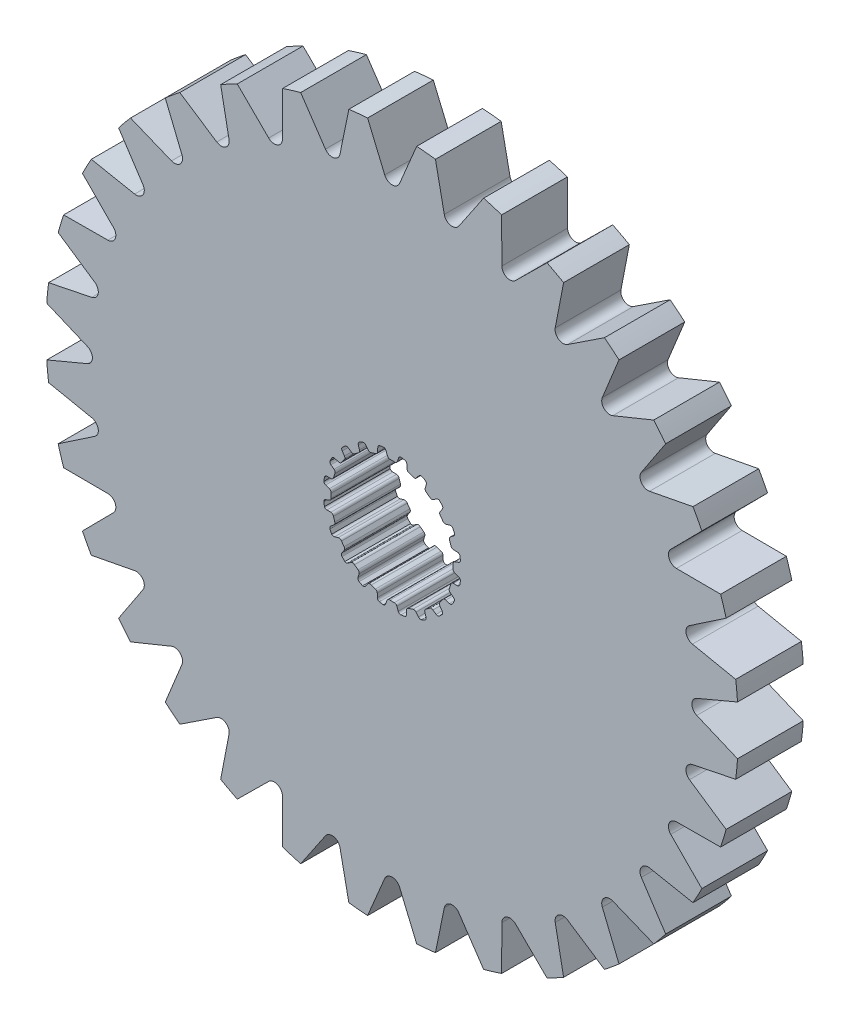
SolidWorks part; units mm, degrees
ref_plane "Front Plane" through (0, 0, 0) normal (0, 0, 1) x (1, 0, 0)
ref_plane "Top Plane" through (0, 0, 0) normal (0, 1, 0) x (1, 0, 0)
ref_plane "Right Plane" through (0, 0, 0) normal (1, 0, 0) x (0, 0, -1)
sketch "Sketch1" plane through (0, 0, 0) normal (0, 0, 1) x (1, 0, 0)
  line L0 (-0.1069, 2.9699) -> (0.1069, 2.9699)
  line L1 (0.3159, 3.2375) -> (0.2537, 3.0575)
  line L2 (-0.2964, 3.2367) -> (-0.2318, 3.0575)
  line L3 (-0.2964, 3.2367) -> (0.3159, 3.2375) construction
  line L4 (0, 3.3252) -> (0, 0) construction
  line L5 (-0.2318, 3.0575) -> (0.2537, 3.0575) construction
  line L6 (-0.4281, 3.3241) -> (0.4281, 3.3263) construction
  line L7 (0.7183, 3.1698) -> (0.7244, 2.9795)
  line L8 (0.816, 2.8576) -> (1.0195, 2.7915)
  line L9 (1.3009, 2.9815) -> (1.1862, 2.8295)
  line L10 (1.6627, 2.7927) -> (1.6097, 2.6099)
  line L11 (1.6591, 2.4655) -> (1.8322, 2.3398)
  line L12 (2.1585, 2.4335) -> (2.0025, 2.3245)
  line L13 (2.4443, 2.1423) -> (2.3374, 1.9847)
  line L14 (2.3398, 1.8322) -> (2.4655, 1.6591)
  line L15 (2.8049, 1.6474) -> (2.6228, 1.5919)
  line L16 (2.9866, 1.2821) -> (2.8363, 1.1653)
  line L17 (2.7915, 1.0195) -> (2.8576, 0.816)
  line L18 (3.1767, 0.7) -> (2.9863, 0.7035)
  line L19 (3.2367, 0.2964) -> (3.0575, 0.2318)
  line L20 (2.9699, 0.1069) -> (2.9699, -0.1069)
  line L21 (3.2375, -0.3159) -> (3.0575, -0.2537)
  line L22 (3.1698, -0.7183) -> (2.9795, -0.7244)
  line L23 (2.8576, -0.816) -> (2.7915, -1.0195)
  line L24 (2.9815, -1.3009) -> (2.8295, -1.1862)
  line L25 (2.7927, -1.6627) -> (2.6099, -1.6097)
  line L26 (2.4655, -1.6591) -> (2.3398, -1.8322)
  line L27 (2.4335, -2.1585) -> (2.3245, -2.0025)
  line L28 (2.1423, -2.4443) -> (1.9847, -2.3374)
  line L29 (1.8322, -2.3398) -> (1.6591, -2.4655)
  line L30 (1.6474, -2.8049) -> (1.5919, -2.6228)
  line L31 (1.2821, -2.9866) -> (1.1653, -2.8363)
  line L32 (1.0195, -2.7915) -> (0.816, -2.8576)
  line L33 (0.7, -3.1767) -> (0.7035, -2.9863)
  line L34 (0.2964, -3.2367) -> (0.2318, -3.0575)
  line L35 (0.1069, -2.9699) -> (-0.1069, -2.9699)
  line L36 (-0.3159, -3.2375) -> (-0.2537, -3.0575)
  line L37 (-0.7183, -3.1698) -> (-0.7244, -2.9795)
  line L38 (-0.816, -2.8576) -> (-1.0195, -2.7915)
  line L39 (-1.3009, -2.9815) -> (-1.1862, -2.8295)
  line L40 (-1.6627, -2.7927) -> (-1.6097, -2.6099)
  line L41 (-1.6591, -2.4655) -> (-1.8322, -2.3398)
  line L42 (-2.1585, -2.4335) -> (-2.0025, -2.3245)
  line L43 (-2.4443, -2.1423) -> (-2.3374, -1.9847)
  line L44 (-2.3398, -1.8322) -> (-2.4655, -1.6591)
  line L45 (-2.8049, -1.6474) -> (-2.6228, -1.5919)
  line L46 (-2.9866, -1.2821) -> (-2.8363, -1.1653)
  line L47 (-2.7915, -1.0195) -> (-2.8576, -0.816)
  line L48 (-3.1767, -0.7) -> (-2.9863, -0.7035)
  line L49 (-3.2367, -0.2964) -> (-3.0575, -0.2318)
  line L50 (-2.9699, -0.1069) -> (-2.9699, 0.1069)
  line L51 (-3.2375, 0.3159) -> (-3.0575, 0.2537)
  line L52 (-3.1698, 0.7183) -> (-2.9795, 0.7244)
  line L53 (-2.8576, 0.816) -> (-2.7915, 1.0195)
  line L54 (-2.9815, 1.3009) -> (-2.8295, 1.1862)
  line L55 (-2.7927, 1.6627) -> (-2.6099, 1.6097)
  line L56 (-2.4655, 1.6591) -> (-2.3398, 1.8322)
  line L57 (-2.4335, 2.1585) -> (-2.3245, 2.0025)
  line L58 (-2.1423, 2.4443) -> (-1.9847, 2.3374)
  line L59 (-1.8322, 2.3398) -> (-1.6591, 2.4655)
  line L60 (-1.6474, 2.8049) -> (-1.5919, 2.6228)
  line L61 (-1.2821, 2.9866) -> (-1.1653, 2.8363)
  line L62 (-1.0195, 2.7915) -> (-0.816, 2.8576)
  line L63 (-0.7, 3.1767) -> (-0.7035, 2.9863)
  line L64 (0.4281, 3.3263) -> (0.62, 3.2938)
  line L65 (1.4351, 3.0312) -> (1.6075, 2.9409)
  line L66 (2.3015, 2.4394) -> (2.4376, 2.3003)
  line L67 (2.9427, 1.6088) -> (3.0291, 1.4344)
  line L68 (3.2958, 0.6207) -> (3.3241, 0.4281)
  line L69 (3.3263, -0.4281) -> (3.2938, -0.62)
  line L70 (3.0312, -1.4351) -> (2.9409, -1.6075)
  line L71 (2.4394, -2.3015) -> (2.3003, -2.4376)
  line L72 (1.6088, -2.9427) -> (1.4344, -3.0291)
  line L73 (0.6207, -3.2958) -> (0.4281, -3.3241)
  line L74 (-0.4281, -3.3263) -> (-0.62, -3.2938)
  line L75 (-1.4351, -3.0312) -> (-1.6075, -2.9409)
  line L76 (-2.3015, -2.4394) -> (-2.4376, -2.3003)
  line L77 (-2.9427, -1.6088) -> (-3.0291, -1.4344)
  line L78 (-3.2958, -0.6207) -> (-3.3241, -0.4281)
  line L79 (-3.3263, 0.4281) -> (-3.2938, 0.62)
  line L80 (-3.0312, 1.4351) -> (-2.9409, 1.6075)
  line L81 (-2.4394, 2.3015) -> (-2.3003, 2.4376)
  line L82 (-1.6088, 2.9427) -> (-1.4344, 3.0291)
  line L83 (-0.6207, 3.2958) -> (-0.4281, 3.3241)
  arc A0 (0.2537, 3.0575) -> (0.1069, 2.9699) centre (0.1283, 3.1009) cw
  arc A1 (-0.2318, 3.0575) -> (-0.1069, 2.9699) centre (-0.1069, 3.1026) ccw
  arc A2 (0.62, 3.2938) -> (0.7183, 3.1698) centre (0.5856, 3.1656) cw
  arc A3 (0.7244, 2.9795) -> (0.816, 2.8576) centre (0.857, 2.9838) ccw
  arc A4 (-0.4281, 3.3241) -> (-0.2964, 3.2367) centre (-0.4213, 3.1916) cw
  arc A5 (0.4281, 3.3263) -> (0.3159, 3.2375) centre (0.4413, 3.1942) ccw
  arc A6 (1.1862, 2.8295) -> (1.0195, 2.7915) centre (1.0802, 2.9095) cw
  arc A7 (1.4351, 3.0312) -> (1.3009, 2.9815) centre (1.4068, 2.9015) ccw
  arc A8 (1.6075, 2.9409) -> (1.6627, 2.7927) centre (1.5352, 2.8297) cw
  arc A9 (1.6097, 2.6099) -> (1.6591, 2.4655) centre (1.7371, 2.5729) ccw
  arc A10 (2.0025, 2.3245) -> (1.8322, 2.3398) centre (1.9264, 2.4332) cw
  arc A11 (2.3015, 2.4394) -> (2.1585, 2.4335) centre (2.2346, 2.3248) ccw
  arc A12 (2.4376, 2.3003) -> (2.4443, 2.1423) centre (2.3345, 2.2168) cw
  arc A13 (2.3374, 1.9847) -> (2.3398, 1.8322) centre (2.4472, 1.9102) ccw
  arc A14 (2.6228, 1.5919) -> (2.4655, 1.6591) centre (2.5841, 1.7189) cw
  arc A15 (2.9427, 1.6088) -> (2.8049, 1.6474) centre (2.8436, 1.5205) ccw
  arc A16 (3.0291, 1.4344) -> (2.9866, 1.2821) centre (2.9052, 1.3869) cw
  arc A17 (2.8363, 1.1653) -> (2.7915, 1.0195) centre (2.9177, 1.0605) ccw
  arc A18 (2.9863, 0.7035) -> (2.8576, 0.816) centre (2.9887, 0.8362) cw
  arc A19 (3.2958, 0.6207) -> (3.1767, 0.7) centre (3.1743, 0.5673) ccw
  arc A20 (3.3241, 0.4281) -> (3.2367, 0.2964) centre (3.1916, 0.4213) cw
  arc A21 (3.0575, 0.2318) -> (2.9699, 0.1069) centre (3.1026, 0.1069) ccw
  arc A22 (3.0575, -0.2537) -> (2.9699, -0.1069) centre (3.1009, -0.1283) cw
  arc A23 (3.3263, -0.4281) -> (3.2375, -0.3159) centre (3.1942, -0.4413) ccw
  arc A24 (3.2938, -0.62) -> (3.1698, -0.7183) centre (3.1656, -0.5856) cw
  arc A25 (2.9795, -0.7244) -> (2.8576, -0.816) centre (2.9838, -0.857) ccw
  arc A26 (2.8295, -1.1862) -> (2.7915, -1.0195) centre (2.9095, -1.0802) cw
  arc A27 (3.0312, -1.4351) -> (2.9815, -1.3009) centre (2.9015, -1.4068) ccw
  arc A28 (2.9409, -1.6075) -> (2.7927, -1.6627) centre (2.8297, -1.5352) cw
  arc A29 (2.6099, -1.6097) -> (2.4655, -1.6591) centre (2.5729, -1.7371) ccw
  arc A30 (2.3245, -2.0025) -> (2.3398, -1.8322) centre (2.4332, -1.9264) cw
  arc A31 (2.4394, -2.3015) -> (2.4335, -2.1585) centre (2.3248, -2.2346) ccw
  arc A32 (2.3003, -2.4376) -> (2.1423, -2.4443) centre (2.2168, -2.3345) cw
  arc A33 (1.9847, -2.3374) -> (1.8322, -2.3398) centre (1.9102, -2.4472) ccw
  arc A34 (1.5919, -2.6228) -> (1.6591, -2.4655) centre (1.7189, -2.5841) cw
  arc A35 (1.6088, -2.9427) -> (1.6474, -2.8049) centre (1.5205, -2.8436) ccw
  arc A36 (1.4344, -3.0291) -> (1.2821, -2.9866) centre (1.3869, -2.9052) cw
  arc A37 (1.1653, -2.8363) -> (1.0195, -2.7915) centre (1.0605, -2.9177) ccw
  arc A38 (0.7035, -2.9863) -> (0.816, -2.8576) centre (0.8362, -2.9887) cw
  arc A39 (0.6207, -3.2958) -> (0.7, -3.1767) centre (0.5673, -3.1743) ccw
  arc A40 (0.4281, -3.3241) -> (0.2964, -3.2367) centre (0.4213, -3.1916) cw
  arc A41 (0.2318, -3.0575) -> (0.1069, -2.9699) centre (0.1069, -3.1026) ccw
  arc A42 (-0.2537, -3.0575) -> (-0.1069, -2.9699) centre (-0.1283, -3.1009) cw
  arc A43 (-0.4281, -3.3263) -> (-0.3159, -3.2375) centre (-0.4413, -3.1942) ccw
  arc A44 (-0.62, -3.2938) -> (-0.7183, -3.1698) centre (-0.5856, -3.1656) cw
  arc A45 (-0.7244, -2.9795) -> (-0.816, -2.8576) centre (-0.857, -2.9838) ccw
  arc A46 (-1.1862, -2.8295) -> (-1.0195, -2.7915) centre (-1.0802, -2.9095) cw
  arc A47 (-1.4351, -3.0312) -> (-1.3009, -2.9815) centre (-1.4068, -2.9015) ccw
  arc A48 (-1.6075, -2.9409) -> (-1.6627, -2.7927) centre (-1.5352, -2.8297) cw
  arc A49 (-1.6097, -2.6099) -> (-1.6591, -2.4655) centre (-1.7371, -2.5729) ccw
  arc A50 (-2.0025, -2.3245) -> (-1.8322, -2.3398) centre (-1.9264, -2.4332) cw
  arc A51 (-2.3015, -2.4394) -> (-2.1585, -2.4335) centre (-2.2346, -2.3248) ccw
  arc A52 (-2.4376, -2.3003) -> (-2.4443, -2.1423) centre (-2.3345, -2.2168) cw
  arc A53 (-2.3374, -1.9847) -> (-2.3398, -1.8322) centre (-2.4472, -1.9102) ccw
  arc A54 (-2.6228, -1.5919) -> (-2.4655, -1.6591) centre (-2.5841, -1.7189) cw
  arc A55 (-2.9427, -1.6088) -> (-2.8049, -1.6474) centre (-2.8436, -1.5205) ccw
  arc A56 (-3.0291, -1.4344) -> (-2.9866, -1.2821) centre (-2.9052, -1.3869) cw
  arc A57 (-2.8363, -1.1653) -> (-2.7915, -1.0195) centre (-2.9177, -1.0605) ccw
  arc A58 (-2.9863, -0.7035) -> (-2.8576, -0.816) centre (-2.9887, -0.8362) cw
  arc A59 (-3.2958, -0.6207) -> (-3.1767, -0.7) centre (-3.1743, -0.5673) ccw
  arc A60 (-3.3241, -0.4281) -> (-3.2367, -0.2964) centre (-3.1916, -0.4213) cw
  arc A61 (-3.0575, -0.2318) -> (-2.9699, -0.1069) centre (-3.1026, -0.1069) ccw
  arc A62 (-3.0575, 0.2537) -> (-2.9699, 0.1069) centre (-3.1009, 0.1283) cw
  arc A63 (-3.3263, 0.4281) -> (-3.2375, 0.3159) centre (-3.1942, 0.4413) ccw
  arc A64 (-3.2938, 0.62) -> (-3.1698, 0.7183) centre (-3.1656, 0.5856) cw
  arc A65 (-2.9795, 0.7244) -> (-2.8576, 0.816) centre (-2.9838, 0.857) ccw
  arc A66 (-2.8295, 1.1862) -> (-2.7915, 1.0195) centre (-2.9095, 1.0802) cw
  arc A67 (-3.0312, 1.4351) -> (-2.9815, 1.3009) centre (-2.9015, 1.4068) ccw
  arc A68 (-2.9409, 1.6075) -> (-2.7927, 1.6627) centre (-2.8297, 1.5352) cw
  arc A69 (-2.6099, 1.6097) -> (-2.4655, 1.6591) centre (-2.5729, 1.7371) ccw
  arc A70 (-2.3245, 2.0025) -> (-2.3398, 1.8322) centre (-2.4332, 1.9264) cw
  arc A71 (-2.4394, 2.3015) -> (-2.4335, 2.1585) centre (-2.3248, 2.2346) ccw
  arc A72 (-2.3003, 2.4376) -> (-2.1423, 2.4443) centre (-2.2168, 2.3345) cw
  arc A73 (-1.9847, 2.3374) -> (-1.8322, 2.3398) centre (-1.9102, 2.4472) ccw
  arc A74 (-1.5919, 2.6228) -> (-1.6591, 2.4655) centre (-1.7189, 2.5841) cw
  arc A75 (-1.6088, 2.9427) -> (-1.6474, 2.8049) centre (-1.5205, 2.8436) ccw
  arc A76 (-1.4344, 3.0291) -> (-1.2821, 2.9866) centre (-1.3869, 2.9052) cw
  arc A77 (-1.1653, 2.8363) -> (-1.0195, 2.7915) centre (-1.0605, 2.9177) ccw
  arc A78 (-0.7035, 2.9863) -> (-0.816, 2.8576) centre (-0.8362, 2.9887) cw
  arc A79 (-0.6207, 3.2958) -> (-0.7, 3.1767) centre (-0.5673, 3.1743) ccw
  circle A80 centre (0, 0) radius 16.8606
  point P14 (0, 2.9699)
  point P247 (0, 0)
  dimension "D4" = 0.1327
  dimension "D8" = 20
  dimension "D9" = 33.7212
  dimension "D1" = 2.9699
  dimension "D2" = 0.2139
  dimension "D3" = 0.1904
  dimension "D5" = 0.0877
  dimension "D6" = 0.4855
  dimension "D7" = 0.8563
extrude "Boss-Extrude1" add sketch "Sketch1" along normal mid plane 3.2004
sketch "Sketch2" plane through (0, 0, 1.6002) normal (0, 0, 1) x (1, 0, 0)
  line L0 (0, 16.8181) -> (0, 0) construction
  line L1 (1.557, 31.6527) -> (0, 0) construction
  line L2 (-1.1958, 16.8181) -> (1.1958, 16.8181) construction
  line L3 (-0.7785, 15.8263) -> (0.7785, 15.8263) construction
  line L4 (-1.1958, 16.8181) -> (-0.3613, 14.8345)
  line L5 (1.1958, 16.8181) -> (0.3613, 14.8345)
  line L6 (4.4538, 16.2617) -> (3.2484, 14.479)
  line L7 (2.1083, 16.7283) -> (2.5398, 14.62)
  line L8 (7.5408, 15.0803) -> (6.0107, 13.5671)
  line L9 (5.3313, 15.9955) -> (5.3432, 13.8436)
  line L10 (10.3379, 13.3195) -> (8.542, 12.1338)
  line L11 (8.3494, 14.6481) -> (7.9413, 12.5352)
  line L12 (12.7378, 11.0467) -> (10.7451, 10.2342)
  line L13 (11.0467, 12.7378) -> (10.2342, 10.7451)
  line L14 (14.6481, 8.3494) -> (12.5352, 7.9413)
  line L15 (13.3195, 10.3379) -> (12.1338, 8.542)
  line L16 (15.9955, 5.3313) -> (13.8436, 5.3432)
  line L17 (15.0803, 7.5408) -> (13.5671, 6.0107)
  line L18 (16.7283, 2.1083) -> (14.62, 2.5398)
  line L19 (16.2617, 4.4538) -> (14.479, 3.2484)
  line L20 (16.8181, -1.1958) -> (14.8345, -0.3613)
  line L21 (16.8181, 1.1958) -> (14.8345, 0.3613)
  line L22 (16.2617, -4.4538) -> (14.479, -3.2484)
  line L23 (16.7283, -2.1083) -> (14.62, -2.5398)
  line L24 (15.0803, -7.5408) -> (13.5671, -6.0107)
  line L25 (15.9955, -5.3313) -> (13.8436, -5.3432)
  line L26 (13.3195, -10.3379) -> (12.1338, -8.542)
  line L27 (14.6481, -8.3494) -> (12.5352, -7.9413)
  line L28 (11.0467, -12.7378) -> (10.2342, -10.7451)
  line L29 (12.7378, -11.0467) -> (10.7451, -10.2342)
  line L30 (8.3494, -14.6481) -> (7.9413, -12.5352)
  line L31 (10.3379, -13.3195) -> (8.542, -12.1338)
  line L32 (5.3313, -15.9955) -> (5.3432, -13.8436)
  line L33 (7.5408, -15.0803) -> (6.0107, -13.5671)
  line L34 (2.1083, -16.7283) -> (2.5398, -14.62)
  line L35 (4.4538, -16.2617) -> (3.2484, -14.479)
  line L36 (-1.1958, -16.8181) -> (-0.3613, -14.8345)
  line L37 (1.1958, -16.8181) -> (0.3613, -14.8345)
  line L38 (-4.4538, -16.2617) -> (-3.2484, -14.479)
  line L39 (-2.1083, -16.7283) -> (-2.5398, -14.62)
  line L40 (-7.5408, -15.0803) -> (-6.0107, -13.5671)
  line L41 (-5.3313, -15.9955) -> (-5.3432, -13.8436)
  line L42 (-10.3379, -13.3195) -> (-8.542, -12.1338)
  line L43 (-8.3494, -14.6481) -> (-7.9413, -12.5352)
  line L44 (-12.7378, -11.0467) -> (-10.7451, -10.2342)
  line L45 (-11.0467, -12.7378) -> (-10.2342, -10.7451)
  line L46 (-14.6481, -8.3494) -> (-12.5352, -7.9413)
  line L47 (-13.3195, -10.3379) -> (-12.1338, -8.542)
  line L48 (-15.9955, -5.3313) -> (-13.8436, -5.3432)
  line L49 (-15.0803, -7.5408) -> (-13.5671, -6.0107)
  line L50 (-16.7283, -2.1083) -> (-14.62, -2.5398)
  line L51 (-16.2617, -4.4538) -> (-14.479, -3.2484)
  line L52 (-16.8181, 1.1958) -> (-14.8345, 0.3613)
  line L53 (-16.8181, -1.1958) -> (-14.8345, -0.3613)
  line L54 (-16.2617, 4.4538) -> (-14.479, 3.2484)
  line L55 (-16.7283, 2.1083) -> (-14.62, 2.5398)
  line L56 (-15.0803, 7.5408) -> (-13.5671, 6.0107)
  line L57 (-15.9955, 5.3313) -> (-13.8436, 5.3432)
  line L58 (-13.3195, 10.3379) -> (-12.1338, 8.542)
  line L59 (-14.6481, 8.3494) -> (-12.5352, 7.9413)
  line L60 (-11.0467, 12.7378) -> (-10.2342, 10.7451)
  line L61 (-12.7378, 11.0467) -> (-10.7451, 10.2342)
  line L62 (-8.3494, 14.6481) -> (-7.9413, 12.5352)
  line L63 (-10.3379, 13.3195) -> (-8.542, 12.1338)
  line L64 (-5.3313, 15.9955) -> (-5.3432, 13.8436)
  line L65 (-7.5408, 15.0803) -> (-6.0107, 13.5671)
  line L66 (-2.1083, 16.7283) -> (-2.5398, 14.62)
  line L67 (-4.4538, 16.2617) -> (-3.2484, 14.479)
  circle A0 centre (0, 0) radius 16.8606 construction
  arc A1 (-0.3613, 14.8345) -> (0.3613, 14.8345) centre (0, 14.9865) ccw
  arc A2 (-1.1958, 16.8181) -> (1.1958, 16.8181) centre (0, 0) cw
  arc A3 (2.1083, 16.7283) -> (4.4538, 16.2617) centre (0, 0) cw
  arc A4 (2.5398, 14.62) -> (3.2484, 14.479) centre (2.9237, 14.6986) ccw
  arc A5 (5.3313, 15.9955) -> (7.5408, 15.0803) centre (0, 0) cw
  arc A6 (5.3432, 13.8436) -> (6.0107, 13.5671) centre (5.7351, 13.8457) ccw
  arc A7 (8.3494, 14.6481) -> (10.3379, 13.3195) centre (0, 0) cw
  arc A8 (7.9413, 12.5352) -> (8.542, 12.1338) centre (8.3261, 12.4608) ccw
  arc A9 (11.0467, 12.7378) -> (12.7378, 11.0467) centre (0, 0) cw
  arc A10 (10.2342, 10.7451) -> (10.7451, 10.2342) centre (10.5971, 10.5971) ccw
  arc A11 (13.3195, 10.3379) -> (14.6481, 8.3494) centre (0, 0) cw
  arc A12 (12.1338, 8.542) -> (12.5352, 7.9413) centre (12.4608, 8.3261) ccw
  arc A13 (15.0803, 7.5408) -> (15.9955, 5.3313) centre (0, 0) cw
  arc A14 (13.5671, 6.0107) -> (13.8436, 5.3432) centre (13.8457, 5.7351) ccw
  arc A15 (16.2617, 4.4538) -> (16.7283, 2.1083) centre (0, 0) cw
  arc A16 (14.479, 3.2484) -> (14.62, 2.5398) centre (14.6986, 2.9237) ccw
  arc A17 (16.8181, 1.1958) -> (16.8181, -1.1958) centre (0, 0) cw
  arc A18 (14.8345, 0.3613) -> (14.8345, -0.3613) centre (14.9865, 0) ccw
  arc A19 (16.7283, -2.1083) -> (16.2617, -4.4538) centre (0, 0) cw
  arc A20 (14.62, -2.5398) -> (14.479, -3.2484) centre (14.6986, -2.9237) ccw
  arc A21 (15.9955, -5.3313) -> (15.0803, -7.5408) centre (0, 0) cw
  arc A22 (13.8436, -5.3432) -> (13.5671, -6.0107) centre (13.8457, -5.7351) ccw
  arc A23 (14.6481, -8.3494) -> (13.3195, -10.3379) centre (0, 0) cw
  arc A24 (12.5352, -7.9413) -> (12.1338, -8.542) centre (12.4608, -8.3261) ccw
  arc A25 (12.7378, -11.0467) -> (11.0467, -12.7378) centre (0, 0) cw
  arc A26 (10.7451, -10.2342) -> (10.2342, -10.7451) centre (10.5971, -10.5971) ccw
  arc A27 (10.3379, -13.3195) -> (8.3494, -14.6481) centre (0, 0) cw
  arc A28 (8.542, -12.1338) -> (7.9413, -12.5352) centre (8.3261, -12.4608) ccw
  arc A29 (7.5408, -15.0803) -> (5.3313, -15.9955) centre (0, 0) cw
  arc A30 (6.0107, -13.5671) -> (5.3432, -13.8436) centre (5.7351, -13.8457) ccw
  arc A31 (4.4538, -16.2617) -> (2.1083, -16.7283) centre (0, 0) cw
  arc A32 (3.2484, -14.479) -> (2.5398, -14.62) centre (2.9237, -14.6986) ccw
  arc A33 (1.1958, -16.8181) -> (-1.1958, -16.8181) centre (0, 0) cw
  arc A34 (0.3613, -14.8345) -> (-0.3613, -14.8345) centre (0, -14.9865) ccw
  arc A35 (-2.1083, -16.7283) -> (-4.4538, -16.2617) centre (0, 0) cw
  arc A36 (-2.5398, -14.62) -> (-3.2484, -14.479) centre (-2.9237, -14.6986) ccw
  arc A37 (-5.3313, -15.9955) -> (-7.5408, -15.0803) centre (0, 0) cw
  arc A38 (-5.3432, -13.8436) -> (-6.0107, -13.5671) centre (-5.7351, -13.8457) ccw
  arc A39 (-8.3494, -14.6481) -> (-10.3379, -13.3195) centre (0, 0) cw
  arc A40 (-7.9413, -12.5352) -> (-8.542, -12.1338) centre (-8.3261, -12.4608) ccw
  arc A41 (-11.0467, -12.7378) -> (-12.7378, -11.0467) centre (0, 0) cw
  arc A42 (-10.2342, -10.7451) -> (-10.7451, -10.2342) centre (-10.5971, -10.5971) ccw
  arc A43 (-13.3195, -10.3379) -> (-14.6481, -8.3494) centre (0, 0) cw
  arc A44 (-12.1338, -8.542) -> (-12.5352, -7.9413) centre (-12.4608, -8.3261) ccw
  arc A45 (-15.0803, -7.5408) -> (-15.9955, -5.3313) centre (0, 0) cw
  arc A46 (-13.5671, -6.0107) -> (-13.8436, -5.3432) centre (-13.8457, -5.7351) ccw
  arc A47 (-16.2617, -4.4538) -> (-16.7283, -2.1083) centre (0, 0) cw
  arc A48 (-14.479, -3.2484) -> (-14.62, -2.5398) centre (-14.6986, -2.9237) ccw
  arc A49 (-16.8181, -1.1958) -> (-16.8181, 1.1958) centre (0, 0) cw
  arc A50 (-14.8345, -0.3613) -> (-14.8345, 0.3613) centre (-14.9865, 0) ccw
  arc A51 (-16.7283, 2.1083) -> (-16.2617, 4.4538) centre (0, 0) cw
  arc A52 (-14.62, 2.5398) -> (-14.479, 3.2484) centre (-14.6986, 2.9237) ccw
  arc A53 (-15.9955, 5.3313) -> (-15.0803, 7.5408) centre (0, 0) cw
  arc A54 (-13.8436, 5.3432) -> (-13.5671, 6.0107) centre (-13.8457, 5.7351) ccw
  arc A55 (-14.6481, 8.3494) -> (-13.3195, 10.3379) centre (0, 0) cw
  arc A56 (-12.5352, 7.9413) -> (-12.1338, 8.542) centre (-12.4608, 8.3261) ccw
  arc A57 (-12.7378, 11.0467) -> (-11.0467, 12.7378) centre (0, 0) cw
  arc A58 (-10.7451, 10.2342) -> (-10.2342, 10.7451) centre (-10.5971, 10.5971) ccw
  arc A59 (-10.3379, 13.3195) -> (-8.3494, 14.6481) centre (0, 0) cw
  arc A60 (-8.542, 12.1338) -> (-7.9413, 12.5352) centre (-8.3261, 12.4608) ccw
  arc A61 (-7.5408, 15.0803) -> (-5.3313, 15.9955) centre (0, 0) cw
  arc A62 (-6.0107, 13.5671) -> (-5.3432, 13.8436) centre (-5.7351, 13.8457) ccw
  arc A63 (-4.4538, 16.2617) -> (-2.1083, 16.7283) centre (0, 0) cw
  arc A64 (-3.2484, 14.479) -> (-2.5398, 14.62) centre (-2.9237, 14.6986) ccw
  point P9 (0, 15.8263)
  point P171 (0, 0)
  dimension "D1" = 0.9918
  dimension "D2" = 1.557
  dimension "D3" = 20
  dimension "D4" = 32
extrude "Cut-Extrude1" cut sketch "Sketch2" against normal up to surface (3.2004 mm away) up to face at (16.8606, 0, -1.6002)
sketch "Sketch3" plane through (0, 0, 1.6002) normal (0, 0, 1) x (1, 0, 0)
  circle A0 centre (0, 0) radius 15.8688 construction
  circle A1 centre (0, 0) radius 16.8606 construction
  dimension "D1" = 31.7376
